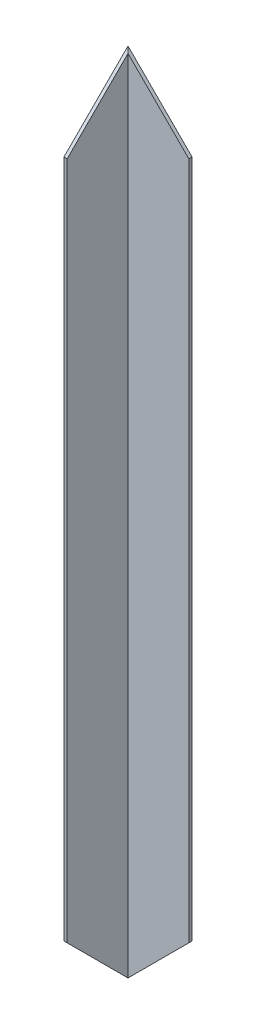
SolidWorks part; units mm, degrees
ref_plane "Plan de face" through (0, 0, 0) normal (0, 0, 1) x (1, 0, 0)
ref_plane "Plan de dessus" through (0, 0, 0) normal (0, 1, 0) x (1, 0, 0)
ref_plane "Plan de droite" through (0, 0, 0) normal (1, 0, 0) x (0, 0, -1)
sketch "Esquisse1" plane through (0, 0, 0) normal (0, 1, 0) x (1, 0, 0)
  line L1 (-20, 20.1136) -> (20, 20.1136)
  line L2 (-20, 20.1136) -> (-20, -19.8864)
  line L3 (-20, -19.8864) -> (-18, -19.8864)
  line L4 (20, 20.1136) -> (20, 18.1136)
  line L5 (-18, 18.1136) -> (20, 18.1136)
  line L6 (-18, 18.1136) -> (-18, -19.8864)
  dimension "D1" = 20
  dimension "D2" = 40
  dimension "D3" = 40
  dimension "D4" = 2
  dimension "D5" = 2
extrude "Boss.-Extru.1" add sketch "Esquisse1" along normal blind 504
sketch "Esquisse2" plane through (0, 0, -20.1136) normal (0, 0, -1) x (-1, 0, 0)
  line L0 (20, 0) -> (-20, 40)
  line L1 (20, 0) -> (-20, 0)
  line L2 (-20, 0) -> (-20, 40)
  dimension "D1" = 45
extrude "Enlèv. mat.-Extru.1" cut sketch "Esquisse2" against normal blind 590
sketch "Esquisse3" plane through (-20, 0, 0) normal (-1, 0, 0) x (0, 0, 1)
  line L0 (-20.1136, 0) -> (19.8864, 40)
  line L1 (19.8864, 504) -> (19.8864, 0) construction
  line L2 (19.8864, 40) -> (19.8864, 0)
  line L3 (19.8864, 0) -> (-20.1136, 0)
  dimension "D1" = 45
extrude "Enlèv. mat.-Extru.2" cut sketch "Esquisse3" against normal blind 590
sketch "Esquisse4" plane through (-20, 0, 0) normal (-1, 0, 0) x (0, 0, 1)
  line L0 (-20.1136, 504) -> (19.8864, 464)
  line L1 (19.8864, 504) -> (19.8864, 40) construction
  line L2 (19.8864, 464) -> (19.8864, 504)
  line L3 (19.8864, 504) -> (-20.1136, 504)
  dimension "D1" = 45
extrude "Enlèv. mat.-Extru.3" cut sketch "Esquisse4" against normal through all
sketch "Esquisse5" plane through (0, 0, -20.1136) normal (0, 0, -1) x (-1, 0, 0)
  line L0 (20, 504) -> (-20, 464)
  line L1 (-20, 504) -> (-20, 40) construction
  line L2 (-20, 464) -> (-20, 504)
  line L3 (-20, 504) -> (20, 504)
  dimension "D1" = 45
extrude "Enlèv. mat.-Extru.4" cut sketch "Esquisse5" against normal through all
